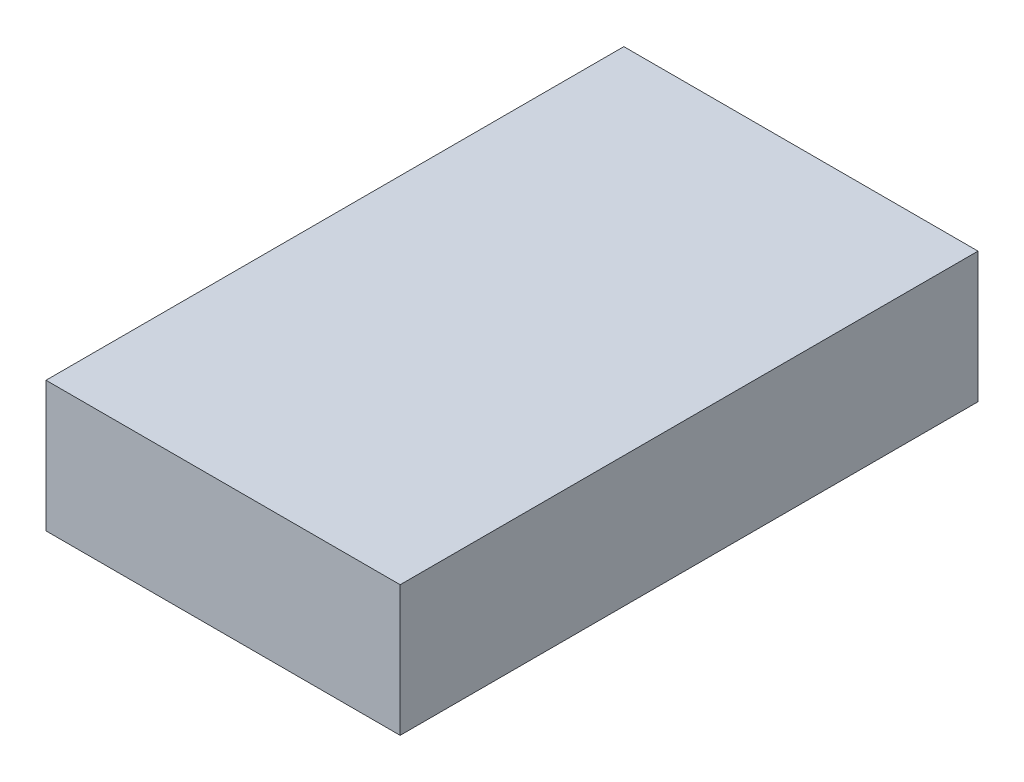
SolidWorks part; units mm, degrees
ref_plane "Front Plane" through (0, 0, 0) normal (0, 0, 1) x (1, 0, 0)
ref_plane "Top Plane" through (0, 0, 0) normal (0, 1, 0) x (1, 0, 0)
ref_plane "Right Plane" through (0, 0, 0) normal (1, 0, 0) x (0, 0, -1)
sketch "Sketch1" plane through (0, 0, 0) normal (0, 1, 0) x (1, 0, 0)
  line L1 (0, 0) -> (48.26, 0)
  line L2 (0, 0) -> (0, 78.74)
  line L3 (0, 78.74) -> (48.26, 78.74)
  line L4 (48.26, 0) -> (48.26, 78.74)
  dimension "D1" = 78.74
  dimension "D2" = 48.26
extrude "Boss-Extrude1" add sketch "Sketch1" along normal blind 17.78
